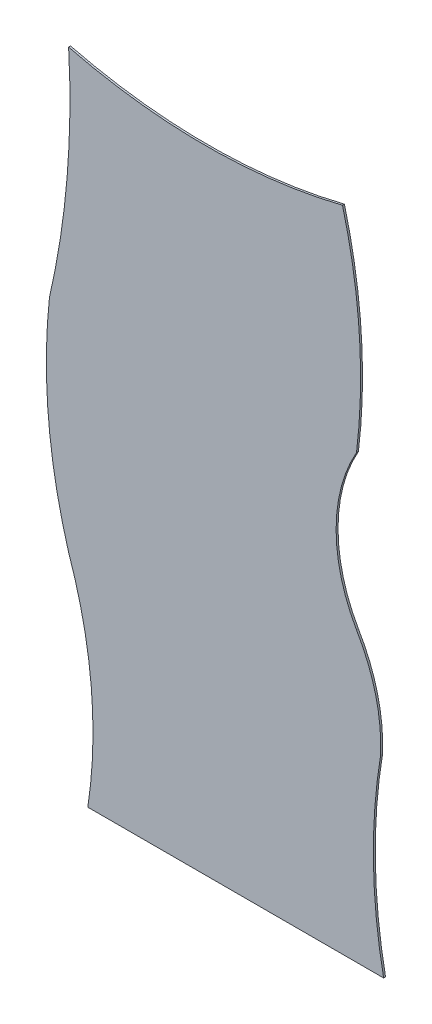
SolidWorks part; units mm, degrees
ref_plane "Alzado" through (0, 0, 0) normal (0, 0, 1) x (1, 0, 0)
ref_plane "Planta" through (0, 0, 0) normal (0, 1, 0) x (1, 0, 0)
ref_plane "Vista lateral" through (0, 0, 0) normal (1, 0, 0) x (0, 0, -1)
sketch "Model" plane through (0, 0, 0) normal (0, 0, 1) x (1, 0, 0)
  line L0 (11.0801, 12.1) -> (26.4942, 12.1)
  arc A0 (9.0801, 34.1) -> (10.0801, 23.1) centre (37.0801, 31.1) ccw
  arc A1 (11.0801, 12.1) -> (10.0801, 23.1) centre (-11.4199, 15.6) ccw
  arc A2 (9.0801, 34.1) -> (10.0801, 45.9) centre (-31.7197, 43.5) ccw
  arc A3 (10.0801, 45.9) -> (24.3506, 45.9) centre (17.2154, 74.471) ccw
  arc A4 (25.0801, 35.1) -> (24.3506, 45.9) centre (-3.4124, 38.6) ccw
  arc A5 (25.0801, 35.1) -> (25.0801, 27.1) centre (32.0801, 31.1) ccw
  arc A6 (26.3349, 22.058) -> (25.0801, 27.1) centre (17.2986, 22.4864) ccw
  arc A7 (26.3349, 22.058) -> (26.4942, 12.1) centre (53.5815, 17.5136) ccw
extrude "Saliente-Extruir1" add sketch "Model" along normal blind 0.1
